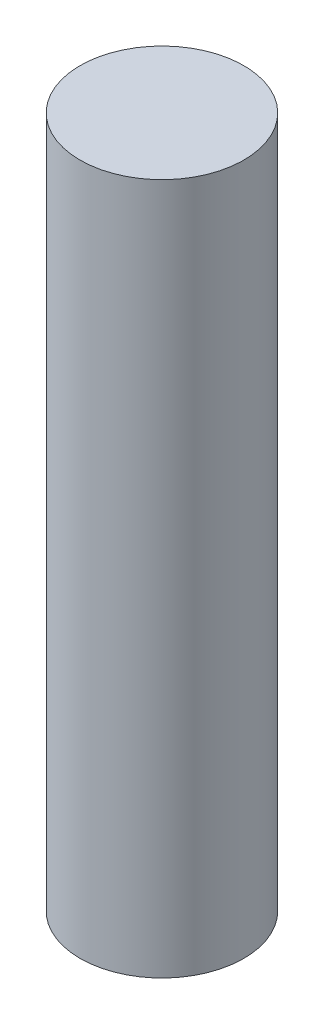
SolidWorks part; units mm, degrees
ref_plane "Front Plane" through (0, 0, 0) normal (0, 0, 1) x (1, 0, 0)
ref_plane "Top Plane" through (0, 0, 0) normal (0, 1, 0) x (1, 0, 0)
ref_plane "Right Plane" through (0, 0, 0) normal (1, 0, 0) x (0, 0, -1)
sketch "Sketch1" plane through (0, 0, 0) normal (0, 1, 0) x (1, 0, 0)
  circle A0 centre (0, 0) radius 9
  dimension "D1" = 18
extrude "Boss-Extrude1" add sketch "Sketch1" along normal blind 76
